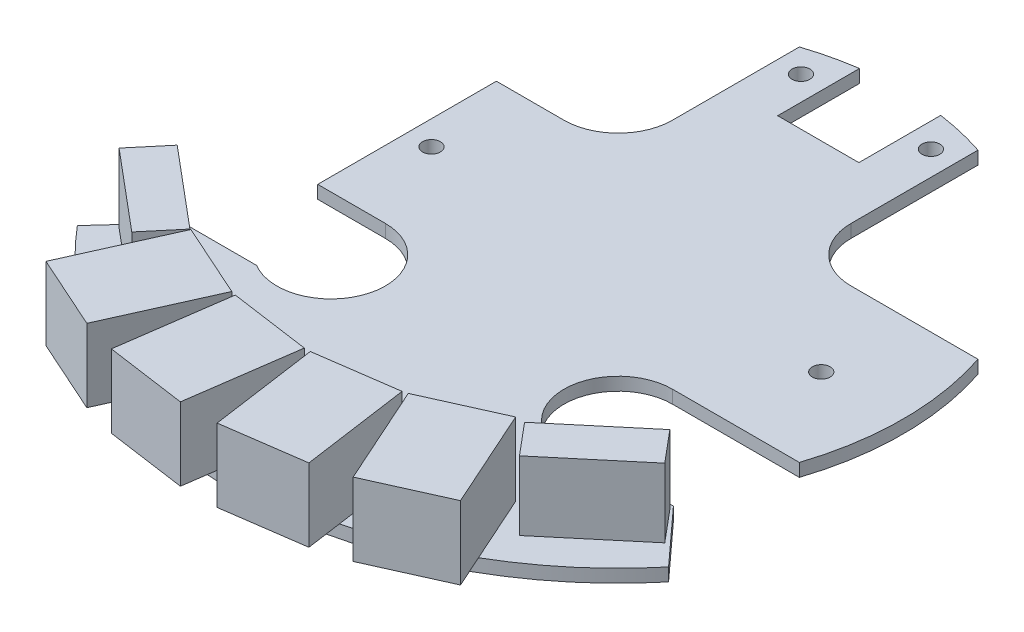
SolidWorks part; units mm, degrees
ref_plane "Front Plane" through (0, 0, 0) normal (0, 0, 1) x (1, 0, 0)
ref_plane "Top Plane" through (0, 0, 0) normal (0, 1, 0) x (1, 0, 0)
ref_plane "Right Plane" through (0, 0, 0) normal (1, 0, 0) x (0, 0, -1)
sketch "Sketch1" plane through (0, 0, 0) normal (0, 1, 0) x (1, 0, 0)
  line L25 (-10.9998, 17.68) -> (-10.9998, 33.3)
  line L26 (-17.6798, 11) -> (-25.9998, 11)
  line L27 (17.6802, 11) -> (33.3002, 11)
  line L28 (11.0002, 17.68) -> (11.0002, 33.2999)
  line L29 (-17.6798, -11) -> (-25.9998, -11)
  line L30 (17.6802, -11) -> (33.3002, -11)
  line L31 (30.2021, -23.4066) -> (36.4, -30.2001)
  line L32 (-30.2021, -23.4066) -> (-36.4, -30.2001)
  line L34 (-30.2021, -23.4066) -> (-21.1191, -23.4066)
  line L35 (21.1195, -23.4066) -> (30.2021, -23.4066)
  line L36 (-5, 24.6335) -> (5, 24.6335)
  line L37 (5, 24.6335) -> (5, 34.7115)
  line L38 (-5, 24.6335) -> (-5, 34.7115)
  line L39 (-25.9998, 11) -> (-25.9998, -11)
  arc A13 (11.0002, 17.68) -> (17.6802, 11) centre (17.6802, 17.68) ccw
  arc A14 (17.6802, -11) -> (21.1195, -23.4066) centre (17.6802, -17.68) ccw
  arc A15 (-21.1191, -23.4066) -> (-17.6798, -11) centre (-17.6798, -17.68) ccw
  arc A16 (-17.6798, 11) -> (-10.9998, 17.68) centre (-17.6798, 17.68) ccw
  arc A17 (-36.4, -30.2001) -> (36.4, -30.2001) centre (0, 0) ccw
  arc A19 (11.0002, 33.2999) -> (5, 34.7115) centre (0, 0) ccw
  arc A20 (-5, 34.7115) -> (-10.9998, 33.3) centre (0, 0) ccw
  arc A21 (33.3002, -11) -> (33.3002, 11) centre (0, 0) ccw
  point P28 (0, 24.6335)
  point P30 (-25.9998, 0)
  dimension "D1" = 22
  dimension "D2" = 22
  dimension "D7" = 6.68
  dimension "D8" = 36.4
  dimension "D11" = 9.196
  dimension "D6" = 47.297
  dimension "D9" = 35.07
  dimension "D3" = 15.62
  dimension "D4" = 15.62
  dimension "D5" = 8.32
  dimension "D10" = 9.083
  dimension "D12" = 10
  dimension "D13" = 10.078
extrude "Boss-Extrude1" add sketch "Sketch1" along normal blind 1.6
sketch "Sketch2" plane through (0, 1.6, 0) normal (0, 1, 0) x (1, 0, 0)
  line L0 (-33.5971, -27.8641) -> (-23.8683, -36.0275)
  line L1 (-33.5971, -27.8641) -> (-30.3317, -23.9725)
  line L2 (-23.8683, -36.0275) -> (-20.6029, -32.1359)
  line L3 (-30.3317, -23.9725) -> (-20.6029, -32.1359)
  line L4 (23.8683, -36.0275) -> (33.5971, -27.8641)
  line L5 (23.8683, -36.0275) -> (20.6029, -32.1359)
  line L6 (33.5971, -27.8641) -> (30.3317, -23.9725)
  line L7 (20.6029, -32.1359) -> (30.3317, -23.9725)
  line L8 (-25.4673, -28.0542) -> (-27.1, -30) construction
  line L9 (-27.1, -30) -> (-22.2356, -34.0817) construction
  line L10 (25.4673, -28.0542) -> (27.1, -30) construction
  line L11 (27.1, -30) -> (22.2356, -34.0817) construction
  line L12 (-27.1, -30) -> (27.1, -30) construction
  point P14 (0, -30)
  dimension "D1" = 12.7
  dimension "D2" = 5.08
  dimension "D3" = 27.1
  dimension "D4" = 30
  dimension "D5" = 50
  dimension "D6" = 50
extrude "Boss-Extrude2" add sketch "Sketch2" along normal blind 8.5
sketch "Sketch3" plane through (0, 1.6, 0) normal (0, 1, 0) x (1, 0, 0)
  line L0 (-25.5179, -44.9397) -> (-19.9902, -32.6233)
  line L1 (-25.5179, -44.9397) -> (-16.3947, -49.0343)
  line L2 (-19.9902, -32.6233) -> (-10.8669, -36.7179)
  line L3 (-16.3947, -49.0343) -> (-10.8669, -36.7179)
  line L4 (-0.3692, -38.2828) -> (-2.2613, -51.6495)
  line L5 (-0.3692, -38.2828) -> (-10.2705, -36.8812)
  line L6 (-2.2613, -51.6495) -> (-12.1626, -50.2479)
  line L7 (-10.2705, -36.8812) -> (-12.1626, -50.2479)
  line L8 (2.2613, -51.6495) -> (0.3692, -38.2828)
  line L9 (2.2613, -51.6495) -> (12.1626, -50.2479)
  line L10 (0.3692, -38.2828) -> (10.2705, -36.8812)
  line L11 (12.1626, -50.2479) -> (10.2705, -36.8812)
  line L12 (16.3947, -49.0343) -> (10.8669, -36.7179)
  line L13 (16.3947, -49.0343) -> (25.5179, -44.9397)
  line L14 (10.8669, -36.7179) -> (19.9902, -32.6233)
  line L15 (25.5179, -44.9397) -> (19.9902, -32.6233)
  line L16 (-5.3198, -37.582) -> (-6.2, -43.8) construction
  line L17 (-6.2, -43.8) -> (-5.0634, -43.9609) construction
  line L18 (5.3198, -37.582) -> (6.2, -43.8) construction
  line L19 (6.2, -43.8) -> (5.0634, -43.9609) construction
  line L20 (15.4286, -34.6706) -> (18, -40.4) construction
  line L21 (18, -40.4) -> (13.4384, -42.4473) construction
  line L22 (-15.4286, -34.6706) -> (-18, -40.4) construction
  line L23 (-18, -40.4) -> (-22.5616, -38.3527) construction
  line L24 (-18, -40.4) -> (18, -40.4) construction
  line L25 (-6.2, -43.8) -> (6.2, -43.8) construction
  point P29 (0, -43.8)
  point P30 (0, -40.4)
  dimension "D1" = 98.057
  dimension "D2" = 81.943
  dimension "D3" = 13.5
  dimension "D4" = 10
  dimension "D5" = 65.829
  dimension "D6" = 65.829
  dimension "D7" = 6.28
  dimension "D8" = 36
  dimension "D9" = 12.4
  dimension "D10" = 3.4
  dimension "D11" = 40.4
extrude "Boss-Extrude3" add sketch "Sketch3" along normal blind 9
sketch "Sketch4" plane through (0, 1.6, 0) normal (0, 1, 0) x (1, 0, 0)
  line L0 (-8, 30.5) -> (8, 30.5) construction
  circle A0 centre (0, -34.8) radius 1.1
  circle A1 centre (25, 0) radius 1.1
  circle A2 centre (-23, 0) radius 1.1
  circle A3 centre (-8, 30.5) radius 1.1
  circle A4 centre (8, 30.5) radius 1.1
  point P10 (0, 30.5)
  dimension "D1" = 2.2
  dimension "D2" = 8
  dimension "D3" = 30.5
  dimension "D4" = 23
  dimension "D5" = 25
  dimension "D6" = 34.8
extrude "Cut-Extrude1" cut sketch "Sketch4" against normal through all
